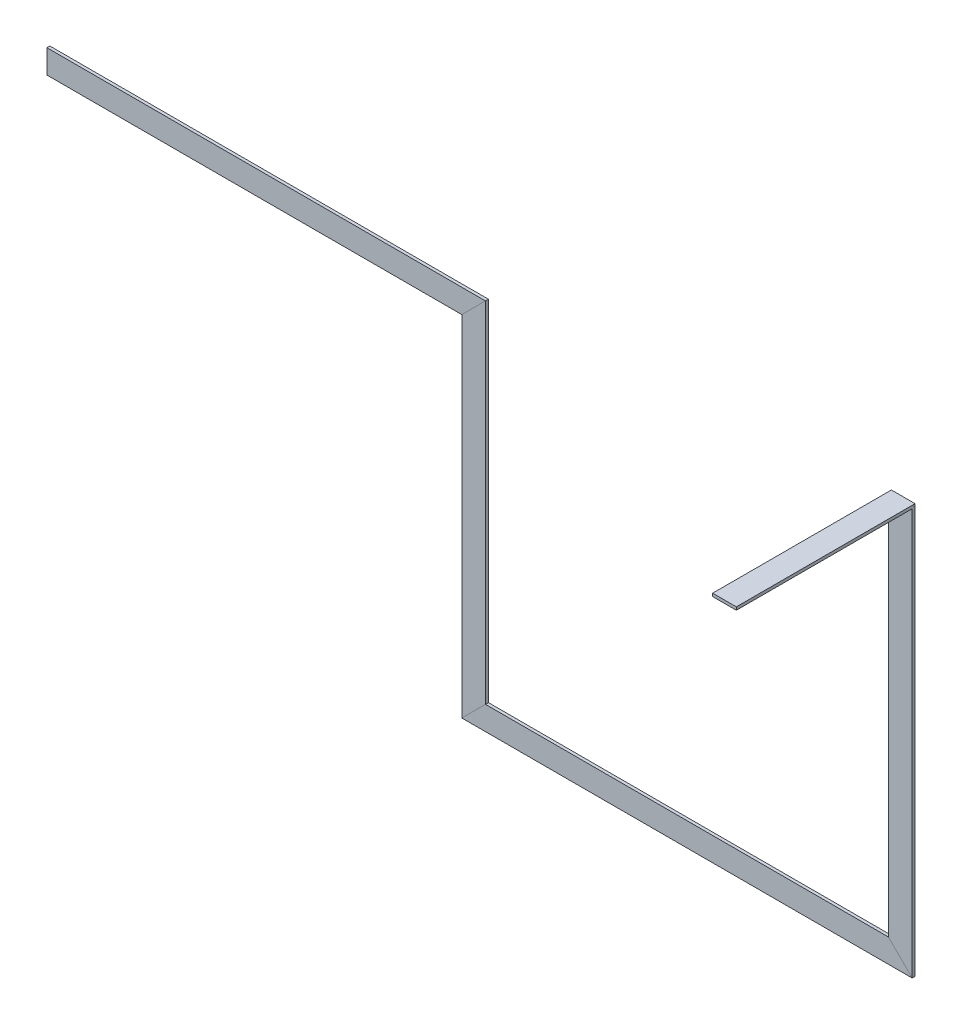
SolidWorks part; units mm, degrees
ref_plane "Alzado" through (0, 0, 0) normal (0, 0, 1) x (1, 0, 0)
ref_plane "Planta" through (0, 0, 0) normal (0, 1, 0) x (1, 0, 0)
ref_plane "Vista lateral" through (0, 0, 0) normal (1, 0, 0) x (0, 0, -1)
sketch3d "Croquis3D1"
  line L0 (867.0219, 367.2895, -44.8905) -> (867.0219, 367.2895, 35.1095)
  line L1 (867.0219, 367.2895, 35.1095) -> (867.0219, -481.9105, 35.1095)
  line L2 (867.0219, -481.9105, 35.1095) -> (-47.9781, -481.9105, 35.1095)
  line L3 (-47.9781, -481.9105, 35.1095) -> (-47.9781, 267.2895, 35.1095)
  line L4 (-47.9781, 267.2895, 35.1095) -> (-962.9681, 267.2895, 35.1095)
  dimension "D1" = 915
  dimension "D5" = 80
  dimension "D2" = 849.2
  dimension "D3" = 749.2
  dimension "D4" = 914.99
ref_plane "Plano1" through (0, 0, -40) normal (0, 0, 1) x (1, 0, 0)
sketch "Croquis1" plane through (0, 0, -40) normal (0, 0, 1) x (1, 0, 0)
  line L1 (841.6219, 370.4645) -> (892.4219, 370.4645)
  line L2 (841.6219, 370.4645) -> (841.6219, 364.1145)
  line L3 (841.6219, 364.1145) -> (892.4219, 364.1145)
  line L4 (892.4219, 370.4645) -> (892.4219, 364.1145)
  line L5 (841.6219, 370.4645) -> (892.4219, 364.1145) construction
  line L6 (841.6219, 364.1145) -> (892.4219, 370.4645) construction
  point P0 (867.0219, 367.2895)
  dimension "D1" = 50.8
  dimension "D2" = 6.35
sweep "Barrer1" add profiles "Croquis1" path "Croquis3D1"
ref_plane "Plano2" through (867.0219, 0, 0) normal (1, 0, 0) x (0, 0, -1)
sketch "Croquis2" plane through (0, 0, 38.2845) normal (0, 0, 1) x (1, 0, 0)
  line L0 (841.6219, 364.1145) -> (892.4219, 364.1145)
  line L1 (892.4219, 370.4645) -> (892.4219, -507.3105) construction
  line L2 (892.4219, 364.1145) -> (892.4219, 370.4645)
  line L3 (892.4219, 370.4645) -> (841.6219, 370.4645)
  line L4 (841.6219, 370.4645) -> (841.6219, 364.1145)
extrude "Saliente-Extruir1" add sketch "Croquis2" along normal blind 377
sketch "Croquis3" plane through (0, 370.4645, 0) normal (0, 1, 0) x (1, 0, 0)
  line L0 (841.6219, -31.9345) -> (892.4219, -31.9345)
  line L1 (892.4219, -31.9345) -> (892.4219, 40)
  line L2 (-482.7763, 40) -> (482.7763, 40) construction
  line L3 (892.4219, 40) -> (841.6219, 40)
  line L4 (841.6219, 40) -> (841.6219, -38.2845) construction
  line L5 (841.6219, 40) -> (841.6219, -31.9345)
extrude "Cortar-Extruir1" cut sketch "Croquis3" against normal blind 10
